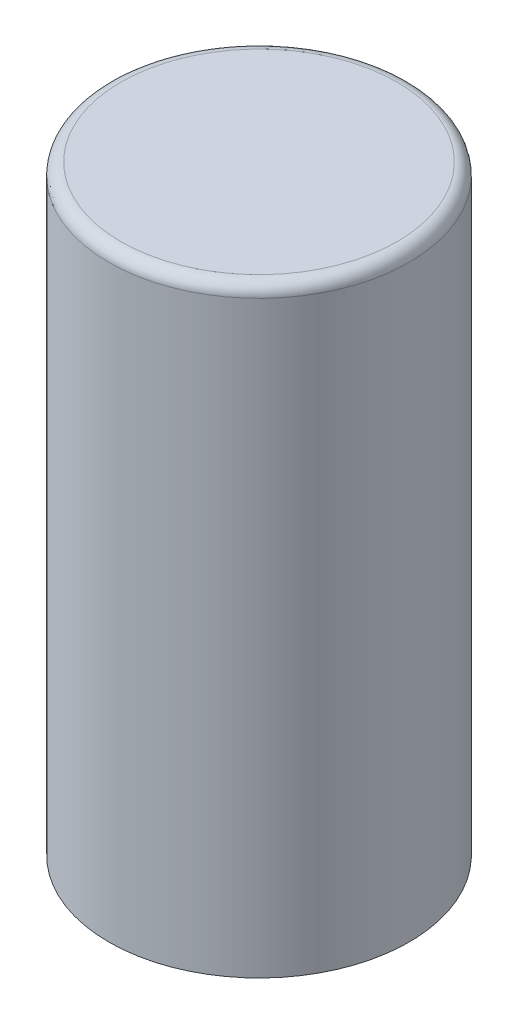
SolidWorks part; units mm, degrees
ref_plane "Front Plane" through (0, 0, 0) normal (0, 0, 1) x (1, 0, 0)
ref_plane "Top Plane" through (0, 0, 0) normal (0, 1, 0) x (1, 0, 0)
ref_plane "Right Plane" through (0, 0, 0) normal (1, 0, 0) x (0, 0, -1)
sketch "Sketch1" plane through (0, 0, 0) normal (0, 1, 0) x (1, 0, 0)
  circle A0 centre (0, 0) radius 6.25
  dimension "D1" = 12.5
extrude "Boss-Extrude1" add sketch "Sketch1" along normal blind 25
fillet "Fillet1" radius 0.5 1 edges at (0, 25, 6.25)
